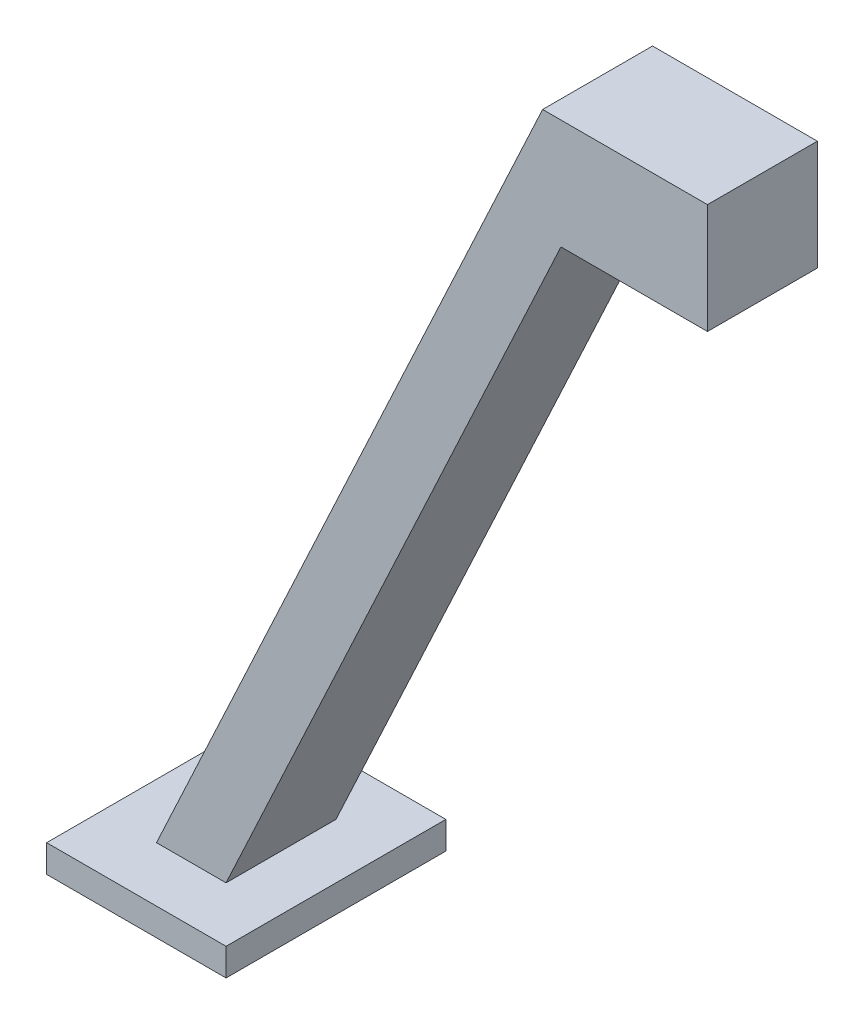
SolidWorks part; units mm, degrees
ref_plane "Front Plane" through (0, 0, 0) normal (0, 0, 1) x (1, 0, 0)
ref_plane "Top Plane" through (0, 0, 0) normal (0, 1, 0) x (1, 0, 0)
ref_plane "Right Plane" through (0, 0, 0) normal (1, 0, 0) x (0, 0, -1)
sketch "Sketch1" plane through (0, 0, 0) normal (0, 0, 1) x (1, 0, 0)
  line L0 (-11.6682, -10) -> (-72.6146, -140.7)
  line L1 (15, -10) -> (-11.6682, -10)
  line L2 (15, -10) -> (15, 10)
  line L3 (15, 10) -> (-15, 10)
  line L7 (-72.6146, -140.7) -> (-85.2726, -140.7)
  line L8 (-85.2726, -140.7) -> (-15, 10)
  point P0 (0, 0)
  point P8 (0, 0)
  point P11 (-13.6421, 10)
  dimension "D1" = 30
  dimension "D2" = 20
  dimension "D3" = 115
  dimension "D5" = 130.7
extrude "Boss-Extrude1" add sketch "Sketch1" along normal blind 20
sketch "Sketch2" plane through (0, -140.7, 0) normal (0, -1, 0) x (1, 0, 0)
  line L8 (-95.2726, -10) -> (-62.6146, -10)
  line L9 (-62.6146, -10) -> (-62.6146, 30)
  line L10 (-62.6146, 30) -> (-95.2726, 30)
  line L11 (-95.2726, 30) -> (-95.2726, -10)
  line L12 (-95.2726, -10) -> (-62.6146, -10)
  line L13 (-62.6146, -10) -> (-62.6146, 30)
  line L14 (-62.6146, 30) -> (-95.2726, 30)
  line L15 (-95.2726, 30) -> (-95.2726, -10)
  dimension "D1" = 10
extrude "Boss-Extrude2" add sketch "Sketch2" along normal blind 5
sketch "Sketch3" plane through (0, -10, 0) normal (0, -1, 0) x (1, 0, 0)
  circle A0 centre (4.737, 9.1808) radius 2.5
  dimension "D1" = 5
extrude "Cut-Extrude1" cut sketch "Sketch3" against normal blind 1
